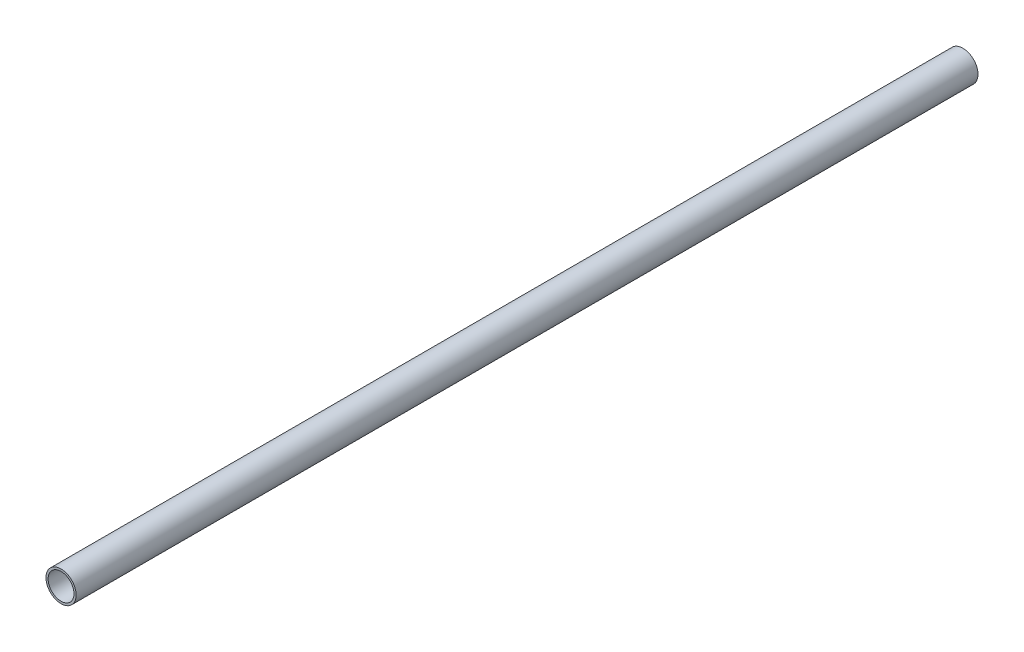
SolidWorks part; units mm, degrees
material "Thornel VCB-20 Carbon Cloth"
ref_plane "Front Plane" through (0, 0, 0) normal (0, 0, 1) x (1, 0, 0)
ref_plane "Top Plane" through (0, 0, 0) normal (0, 1, 0) x (1, 0, 0)
ref_plane "Right Plane" through (0, 0, 0) normal (1, 0, 0) x (0, 0, -1)
sketch "Sketch1" plane through (0, 0, 0) normal (0, 0, 1) x (1, 0, 0)
  circle A0 centre (0, 0) radius 9.525
  circle A1 centre (0, 0) radius 11.1125
  dimension "D1" = 19.05
  dimension "D2" = 22.225
extrude "Boss-Extrude1" add sketch "Sketch1" along normal mid plane 664.718
scale "Scale1" scale about centroid uniform scaling yes scale factor 0.35
